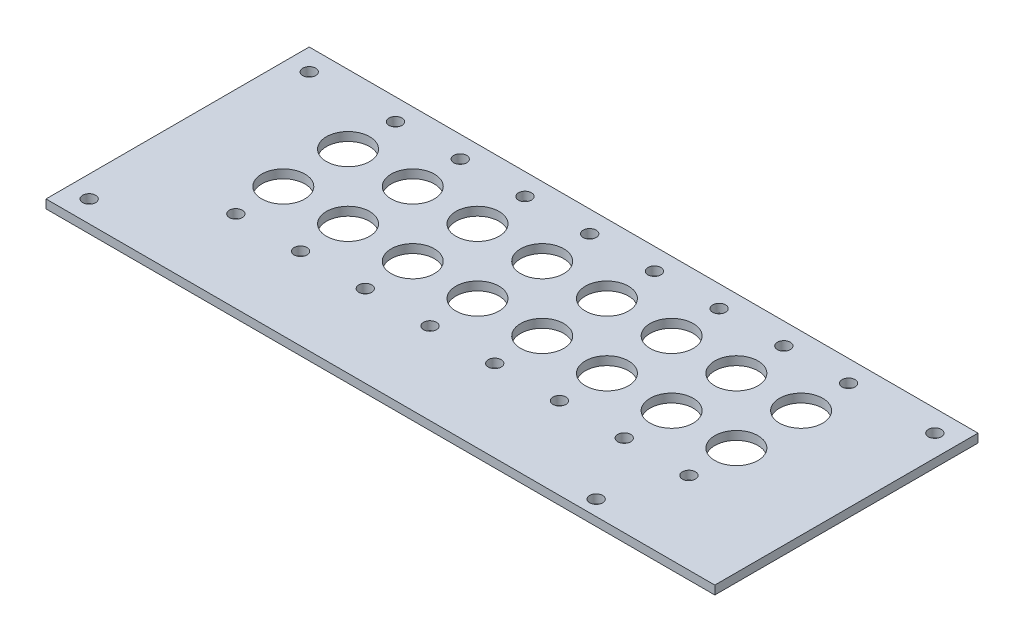
SolidWorks part; units mm, degrees
material "Cuivre"
ref_plane "Plan de face" through (0, 0, 0) normal (0, 0, 1) x (1, 0, 0)
ref_plane "Plan de dessus" through (0, 0, 0) normal (0, 1, 0) x (1, 0, 0)
ref_plane "Plan de droite" through (0, 0, 0) normal (1, 0, 0) x (0, 0, -1)
sketch "Esquisse1" plane through (0, 0, 0) normal (0, 1, 0) x (1, 0, 0)
  line L0 (-52.5, 14.5) -> (-37.5, 14.5) construction
  line L1 (-77.5, -30.5) -> (77.5, -30.5)
  line L2 (-77.5, -30.5) -> (-77.5, 30.5)
  line L3 (-77.5, 30.5) -> (77.5, 30.5)
  line L4 (77.5, -30.5) -> (77.5, 30.5)
  line L5 (-77.5, -30.5) -> (77.5, 30.5) construction
  line L6 (-77.5, 30.5) -> (77.5, -30.5) construction
  line L7 (-52.5, 14.5) -> (-52.5, -0.5) construction
  line L8 (-52.5, 25.5) -> (-37.5, 25.5) construction
  line L9 (-52.5, -11.5) -> (-37.5, -11.5) construction
  circle A0 centre (-52.5, 14.5) radius 5
  circle A1 centre (-37.5, 14.5) radius 5
  circle A2 centre (-22.5, 14.5) radius 5
  circle A3 centre (-7.5, 14.5) radius 5
  circle A4 centre (7.5, 14.5) radius 5
  circle A5 centre (22.5, 14.5) radius 5
  circle A6 centre (37.5, 14.5) radius 5
  circle A7 centre (52.5, 14.5) radius 5
  circle A8 centre (-37.5, -0.5) radius 5
  circle A9 centre (-22.5, -0.5) radius 5
  circle A10 centre (-7.5, -0.5) radius 5
  circle A11 centre (7.5, -0.5) radius 5
  circle A12 centre (22.5, -0.5) radius 5
  circle A13 centre (37.5, -0.5) radius 5
  circle A14 centre (52.5, -0.5) radius 5
  circle A15 centre (-52.5, -0.5) radius 5
  circle A16 centre (-52.5, 25.5) radius 1.5
  circle A17 centre (-37.5, 25.5) radius 1.5
  circle A18 centre (-22.5, 25.5) radius 1.5
  circle A19 centre (-7.5, 25.5) radius 1.5
  circle A20 centre (7.5, 25.5) radius 1.5
  circle A21 centre (22.5, 25.5) radius 1.5
  circle A22 centre (37.5, 25.5) radius 1.5
  circle A23 centre (52.5, 25.5) radius 1.5
  circle A24 centre (-52.5, -11.5) radius 1.5
  circle A25 centre (-37.5, -11.5) radius 1.5
  circle A26 centre (-22.5, -11.5) radius 1.5
  circle A27 centre (-7.5, -11.5) radius 1.5
  circle A28 centre (7.5, -11.5) radius 1.5
  circle A29 centre (22.5, -11.5) radius 1.5
  circle A30 centre (37.5, -11.5) radius 1.5
  circle A31 centre (52.5, -11.5) radius 1.5
  circle A32 centre (46.5, -27) radius 1.5
  circle A33 centre (-72.5, 25.5) radius 1.5
  circle A34 centre (-72.5, -25.5) radius 1.5
  circle A35 centre (72.5, 25.5) radius 1.5
  point P0 (0, 0)
  point P83 (0, 0)
  dimension "D5" = 10
  dimension "D10" = 3
  dimension "D14" = 11
  dimension "D19" = 3
  dimension "D22" = 5
  dimension "D1" = 155
  dimension "D2" = 61
  dimension "D3" = 25
  dimension "D4" = 16
  dimension "D8" = 15
  dimension "D9" = 15
  dimension "D11" = 11
  dimension "D13" = 15
  dimension "D16" = 15
  dimension "D17" = 31
  dimension "D18" = 3.5
  dimension "D20" = 5
  dimension "D21" = 5
  dimension "D23" = 5
  dimension "D24" = 5
  dimension "D25" = 5
  dimension "D6" = 8
  dimension "D7" = 2
  dimension "D12" = 8
  dimension "D15" = 8
extrude "Boss.-Extru.2" add sketch "Esquisse1" along normal blind 2
